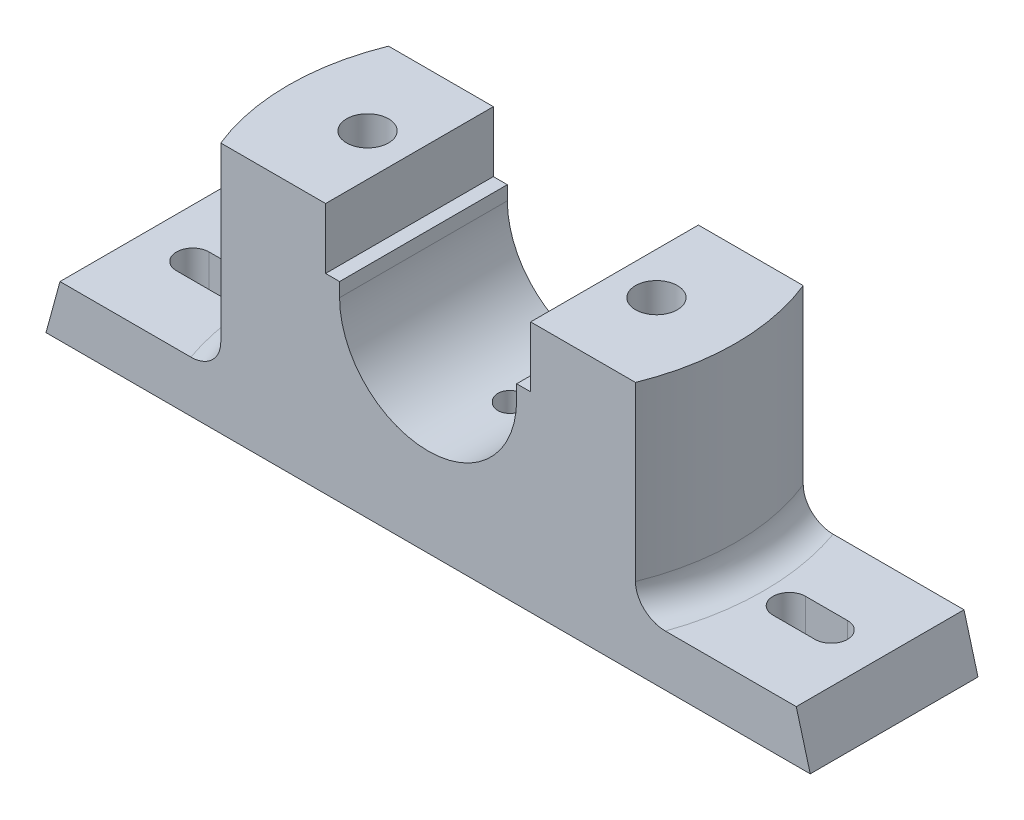
SolidWorks part; units mm, degrees
ref_plane "Front Plane" through (0, 0, 0) normal (0, 0, 1) x (1, 0, 0)
ref_plane "Top Plane" through (0, 0, 0) normal (0, 1, 0) x (1, 0, 0)
ref_plane "Right Plane" through (0, 0, 0) normal (1, 0, 0) x (0, 0, -1)
sketch "Sketch1" plane through (0, 0, 0) normal (0, 0, 1) x (1, 0, 0)
  line L0 (82, 0) -> (-82, 0)
  line L1 (-82, 0) -> (-79, 11)
  line L2 (-79, 11) -> (-50, 11)
  line L3 (-50, 11) -> (-50, 54)
  line L4 (-50, 54) -> (-22, 54)
  line L5 (-22, 54) -> (-22, 41)
  line L6 (-22, 41) -> (-19, 41)
  line L7 (0, 0) -> (0, 71.5482) construction
  line L8 (22, 41) -> (19, 41)
  line L9 (22, 54) -> (22, 41)
  line L10 (50, 54) -> (22, 54)
  line L11 (50, 11) -> (50, 54)
  line L12 (82, 0) -> (79, 11)
  line L13 (79, 11) -> (50, 11)
  line L14 (19, 38) -> (19, 41)
  line L15 (-19, 38) -> (-19, 41)
  arc A0 (-19, 38) -> (19, 38) centre (0, 38) ccw
  dimension "D6" = 16
  dimension "D7" = 19
  dimension "D1" = 3
  dimension "D2" = 11
  dimension "D3" = 164
  dimension "D4" = 54
  dimension "D5" = 13
  dimension "D8" = 38
  dimension "D9" = 44
extrude "Boss-Extrude1" add sketch "Sketch1" along normal mid plane 36
sketch "Sketch2" plane through (0, 54, 0) normal (0, 1, 0) x (1, 0, 0)
  line L0 (-22, -18) -> (-50, -18) construction
  line L1 (-22, 18) -> (-50, 18) construction
  line L2 (-50, -18) -> (-50, 18) construction
  line L3 (50, 18) -> (22, 18) construction
  line L4 (50, -18) -> (50, 18) construction
  line L5 (50, -18) -> (22, -18) construction
  line L6 (-44.4972, -18) -> (-50, -18)
  line L7 (-44.4972, 18) -> (-50, 18)
  line L8 (-50, -18) -> (-50, 18)
  line L9 (50, 18) -> (44.4972, 18)
  line L10 (50, -18) -> (50, 18)
  line L11 (50, -18) -> (44.4972, -18)
  arc A0 (-44.4972, 18) -> (-44.4972, -18) centre (0, 0) ccw
  arc A1 (44.4972, -18) -> (44.4972, 18) centre (0, 0) ccw
  dimension "D1" = 48
extrude "Cut-Extrude1" cut sketch "Sketch2" against normal up to vertex (43 mm away) up to point (-50, 11, 18)
sketch "Sketch4" plane through (0, 11, 0) normal (0, 1, 0) x (1, 0, 0)
  line L0 (-59.5, 0) -> (-68.5, 0) construction
  line L1 (-59.5, -3.5) -> (-68.5, -3.5)
  line L2 (-59.5, 3.5) -> (-68.5, 3.5)
  arc A0 (-59.5, -3.5) -> (-59.5, 3.5) centre (-59.5, 0) ccw
  arc A1 (-68.5, 3.5) -> (-68.5, -3.5) centre (-68.5, 0) ccw
  point P3 (-64, 0)
  dimension "D1" = 16
  dimension "D2" = 9
extrude "Cut-Extrude2" cut sketch "Sketch4" against normal through all
sketch "Sketch6" plane through (0, 0, 0) normal (0, -1, 0) x (1, 0, 0)
  line L0 (29.7, 0) -> (-29.7, 0) construction
  line L1 (-41, 10) -> (-21, 10)
  line L2 (-41, 10) -> (-41, -10)
  line L3 (-41, -10) -> (-21, -10)
  line L4 (-21, 10) -> (-21, -10)
  line L5 (-41, 10) -> (-21, -10) construction
  line L6 (-41, -10) -> (-21, 10) construction
  point P0 (-31, 0)
  dimension "D1" = 20
  dimension "D2" = 20
  dimension "D3" = 31
  dimension "D4" = 0
extrude "Cut-Extrude3" cut sketch "Sketch6" against normal blind 8
sketch "Sketch7" plane through (0, 8, 0) normal (0, -1, 0) x (1, 0, 0)
  circle A0 centre (-31, 0) radius 4.5
  dimension "D1" = 9
extrude "Cut-Extrude4" cut sketch "Sketch7" against normal through all
fillet "Fillet1" radius 6 2 edges at (-48, 11, 0) (48, 11, 0)
mirror "Mirror6" about plane through (0, 0, 0) normal (1, 0, 0) of "Cut-Extrude3", "Cut-Extrude4", "Cut-Extrude2"
hole_wizard "Ø6.0mm Dowel Hole1" positions "3DSketch5" profile "Sketch15" hole size "Ø6.0" standard "ANSI Metric"
sketch3d "3DSketch5"
  point P0 (0, 19, 0)
  dimension "D1" = 0
  dimension "D2" = 0
sketch "Sketch15" plane through (0, 19, 0) normal (1, 0, 0) x (0, 0, 1)
  line L0 (0, 0) -> (0, 7.8026)
  line L1 (0, 7.8026) -> (3, 6)
  line L2 (3, 6) -> (3, 0)
  line L5 (3, 0) -> (0, 0)
  line L10 (0, 7.8026) -> (-3, 6) construction
  line L11 (0, -6.35) -> (0, 107.95) construction
  dimension "Hole Dia." = 6
  dimension "Hole Depth" = 6
  dimension "Drill Angle" = 118
sketch "Sketch16" plane through (0, 11, 0) normal (0, 1, 0) x (1, 0, 0)
  point P0 (38.3663, 18.9371)
  point P2 (-64, 0)
  point P6 (64, 0)
  dimension "D1" = 128
sketch "Sketch17" plane through (0, 0, 0) normal (0, -1, 0) x (-1, 0, 0)
  point P2 (-31, 0)
  point P3 (31, 0)
  dimension "D1" = 62
